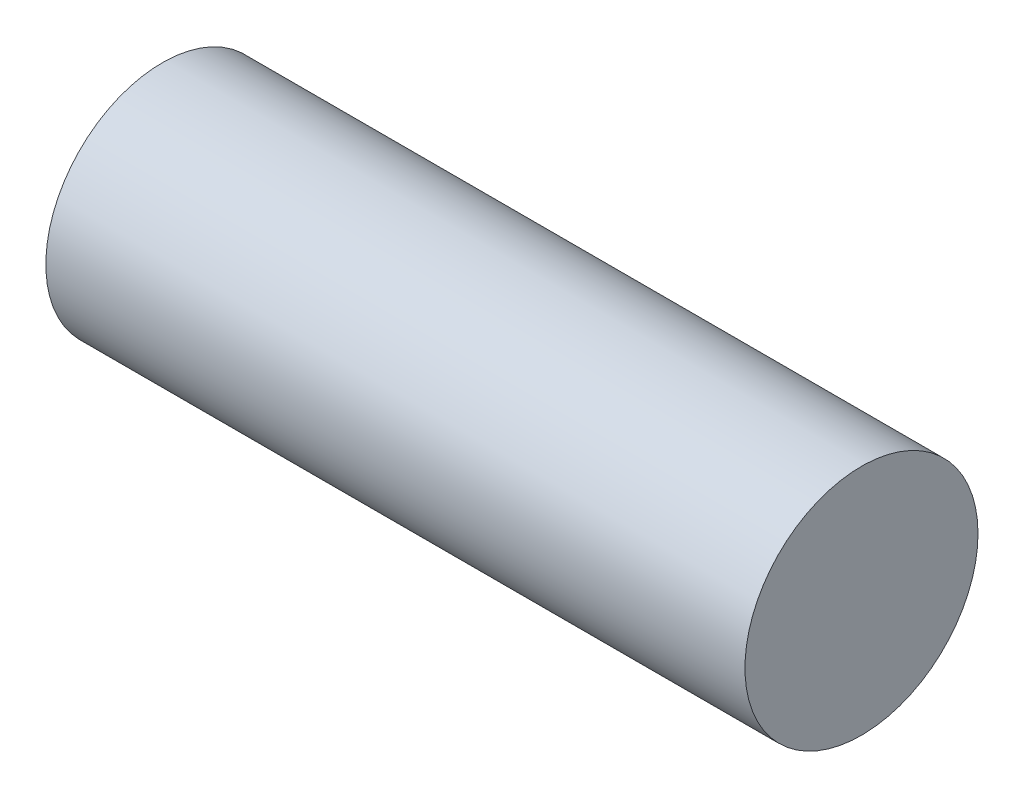
SolidWorks part; units mm, degrees
ref_plane "Alzado" through (0, 0, 0) normal (0, 0, 1) x (1, 0, 0)
ref_plane "Planta" through (0, 0, 0) normal (0, 1, 0) x (1, 0, 0)
ref_plane "Vista lateral" through (0, 0, 0) normal (1, 0, 0) x (0, 0, -1)
sketch "Croquis1" plane through (0, 0, 0) normal (1, 0, 0) x (0, 0, -1)
  circle A0 centre (0, 0) radius 10
  dimension "D1" = 20
extrude "Saliente-Extruir1" add sketch "Croquis1" along normal mid plane 60
